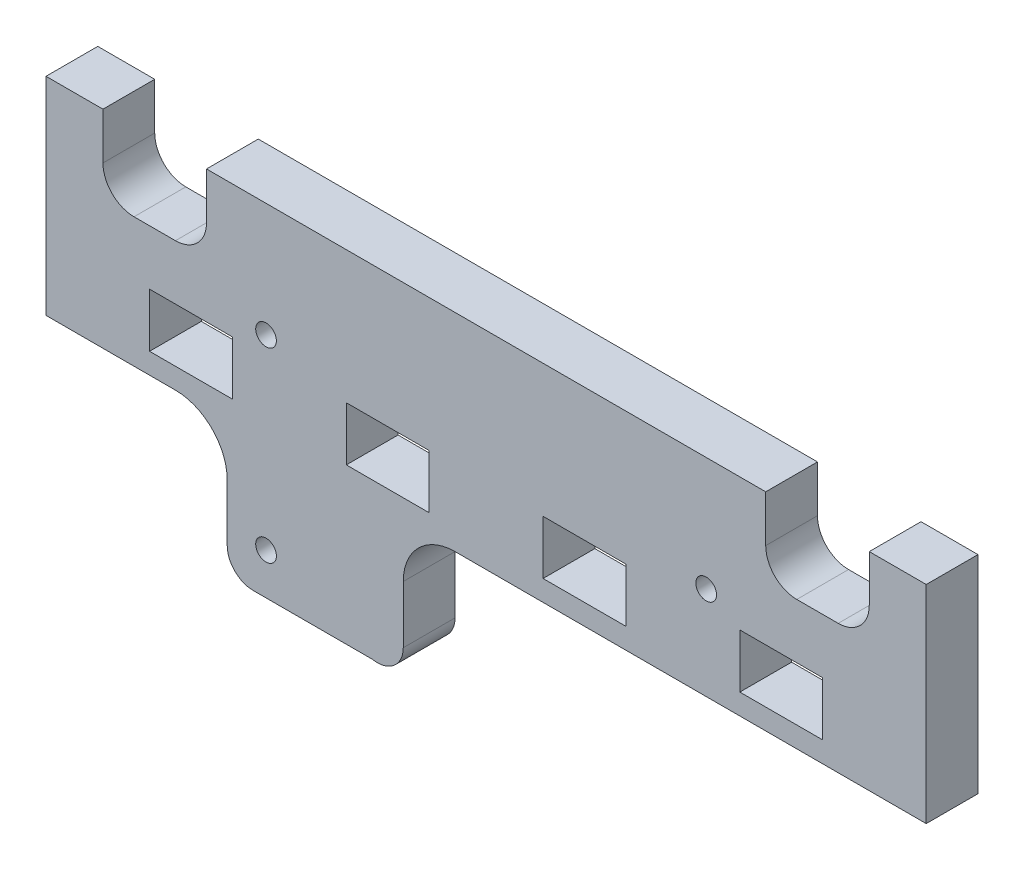
SolidWorks part; units mm, degrees
ref_plane "Front Plane" through (0, 0, 0) normal (0, 0, 1) x (1, 0, 0)
ref_plane "Top Plane" through (0, 0, 0) normal (0, 1, 0) x (1, 0, 0)
ref_plane "Right Plane" through (0, 0, 0) normal (1, 0, 0) x (0, 0, -1)
sketch "Sketch1" plane through (0, 0, 0) normal (0, 0, 1) x (1, 0, 0)
  line L0 (24.4856, 0) -> (69.9856, 0)
  line L1 (-15.0144, 20) -> (69.9856, 20)
  line L2 (-15.0144, 20) -> (-15.0144, 0)
  line L3 (-15.0144, 0) -> (-2.5144, 0)
  line L4 (69.9856, 20) -> (69.9856, 0)
  line L6 (2.4856, -5) -> (2.4856, -10.5)
  line L7 (4.9856, -13) -> (16.5288, -13)
  line L8 (19.4856, -5) -> (19.4856, -10.5421)
  arc A0 (19.4856, -5) -> (24.4856, 0) centre (24.4856, -5) cw
  arc A1 (2.4856, -5) -> (-2.5144, 0) centre (-2.5144, -5) ccw
  arc A2 (16.5288, -13) -> (19.4856, -10.5421) centre (16.9856, -10.5421) ccw
  arc A3 (4.9856, -13) -> (2.4856, -10.5) centre (4.9856, -10.5) cw
  point P14 (41.5288, -13)
  point P17 (-8.4712, -13)
  dimension "D4" = 5
  dimension "D5" = 2.5
  dimension "D1" = 85
  dimension "D2" = 17.5
  dimension "D3" = 17
  dimension "D6" = 20
extrude "Boss-Extrude1" add sketch "Sketch1" along normal blind 5 contours L1 L4 L0 A0 L8 A2 L7 A3 L6 A1 L3 L2
sketch "Sketch2" plane through (0, 0, 5) normal (0, 0, 1) x (1, 0, 0)
  line L0 (4.9856, 4.6) -> (-15.0144, 4.6) construction
  line L1 (-5.0144, 7.2) -> (2.9856, 7.2)
  line L2 (-5.0144, 7.2) -> (-5.0144, 2)
  line L3 (-5.0144, 2) -> (2.9856, 2)
  line L4 (2.9856, 7.2) -> (2.9856, 2)
  line L5 (-15.0144, 20) -> (-15.0144, 0) construction
  line L6 (13.9856, 7.2) -> (21.9856, 7.2)
  line L7 (13.9856, 7.2) -> (13.9856, 2)
  line L8 (13.9856, 2) -> (21.9856, 2)
  line L9 (21.9856, 7.2) -> (21.9856, 2)
  line L10 (32.9856, 7.2) -> (40.9856, 7.2)
  line L11 (32.9856, 7.2) -> (32.9856, 2)
  line L12 (32.9856, 2) -> (40.9856, 2)
  line L13 (40.9856, 7.2) -> (40.9856, 2)
  line L14 (51.9856, 7.2) -> (59.9856, 7.2)
  line L15 (51.9856, 7.2) -> (51.9856, 2)
  line L16 (51.9856, 2) -> (59.9856, 2)
  line L17 (59.9856, 7.2) -> (59.9856, 2)
  line L18 (-15.0144, 0) -> (-2.5144, 0) construction
  point P9 (-5.0144, 4.6)
  point P14 (13.9856, 4.6)
  point P19 (32.9856, 4.6)
  point P24 (51.9856, 4.6)
  dimension "D2" = 5.2
  dimension "D3" = 8
  dimension "D4" = 10
  dimension "D5" = 4.6
  dimension "D6" = 11
  dimension "D1" = 4
extrude "Cut-Extrude1" cut sketch "Sketch2" against normal up to next
sketch "Sketch3" plane through (0, 0, 5) normal (0, 0, 1) x (1, 0, 0)
  line L0 (-15.0144, 20) -> (69.9856, 20) construction
  line L1 (-9.5144, 20) -> (0.4856, 20)
  line L2 (-9.5144, 20) -> (-9.5144, 15.5)
  line L3 (-6.5144, 12.5) -> (-2.5144, 12.5)
  line L4 (0.4856, 20) -> (0.4856, 15.5)
  line L5 (-15.0144, 20) -> (-15.0144, 0) construction
  arc A0 (-2.5144, 12.5) -> (0.4856, 15.5) centre (-2.5144, 15.5) ccw
  arc A1 (-9.5144, 15.5) -> (-6.5144, 12.5) centre (-6.5144, 15.5) ccw
  dimension "D1" = 3
  dimension "D2" = 7.5
  dimension "D3" = 10
  dimension "D4" = 5.5
extrude "Cut-Extrude2" cut sketch "Sketch3" against normal up to next (5 mm away)
ref_plane "Plane1" through (27.4856, 0, 0) normal (1, 0, 0) x (0, 0, -1)
mirror "Mirror1" about plane through (27.4856, 0, 0) normal (1, 0, 0) of "Cut-Extrude2"
sketch "Sketch5" plane through (0, 0, 5) normal (0, 0, 1) x (1, 0, 0)
  line L0 (27.4856, 20) -> (27.4856, -13) construction
  line L1 (0.4856, 20) -> (54.4856, 20) construction
  line L3 (6.2356, 9) -> (6.2356, -9) construction
  circle A0 centre (6.2356, 9) radius 1
  circle A1 centre (48.7356, 9) radius 1
  circle A2 centre (6.2356, -9) radius 1
  dimension "D2" = 2
  dimension "D1" = 11
  dimension "D3" = 21.25
  dimension "D4" = 18
extrude "Cut-Extrude3" cut sketch "Sketch5" against normal up to next
